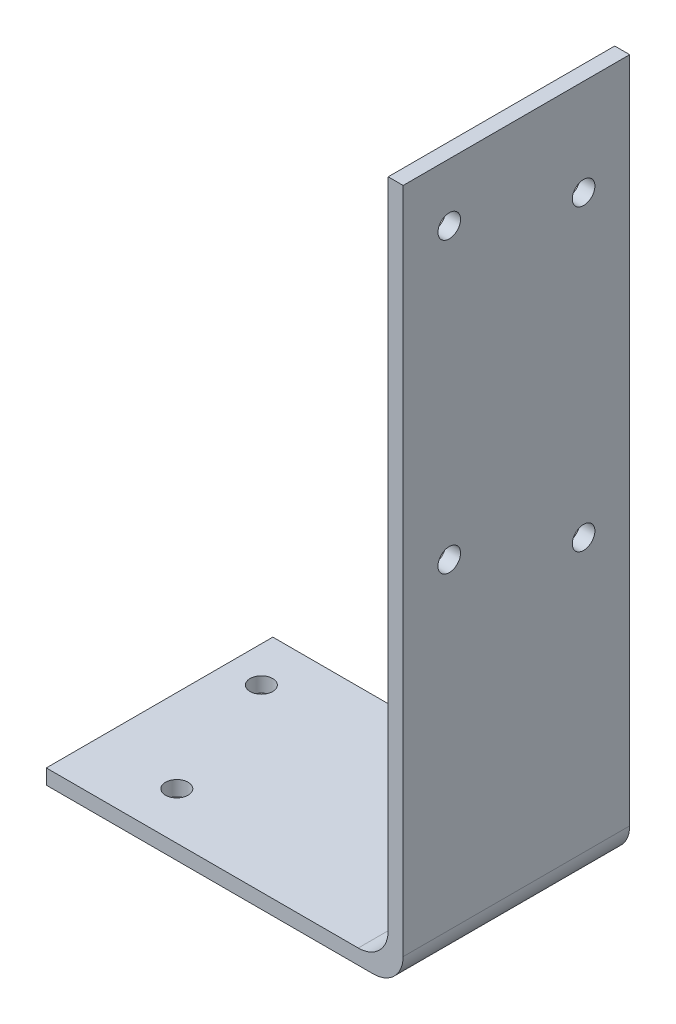
SolidWorks part; units mm, degrees
ref_plane "Front Plane" through (0, 0, 0) normal (0, 0, 1) x (1, 0, 0)
ref_plane "Top Plane" through (0, 0, 0) normal (0, 1, 0) x (1, 0, 0)
ref_plane "Right Plane" through (0, 0, 0) normal (1, 0, 0) x (0, 0, -1)
sketch "Sketch1" plane through (0, 0, 0) normal (0, 0, 1) x (1, 0, 0)
  line L0 (0, 0) -> (113.4872, 0)
  line L1 (113.4872, 0) -> (113.4872, 118.4148)
  line L2 (113.4872, 118.4148) -> (110.9472, 118.4148)
  line L3 (110.9472, 118.4148) -> (110.9472, 2.54)
  line L4 (110.9472, 2.54) -> (0, 2.54)
  line L5 (0, 2.54) -> (0, 0)
  dimension "D1" = 2.54
  dimension "D2" = 113.4872
  dimension "D3" = 118.4148
extrude "Boss-Extrude1" add sketch "Sketch1" along normal blind 38.4429
sketch "Sketch2" plane through (0, 2.54, 0) normal (0, 1, 0) x (1, 0, 0)
  line L0 (16.2052, -38.4429) -> (16.2052, -30.4292) construction
  line L1 (110.9472, -38.4429) -> (0, -38.4429) construction
  line L2 (16.2052, -30.4292) -> (67.0687, -30.4292) construction
  line L3 (9.8806, 0) -> (9.8806, -8.0137) construction
  line L4 (110.9472, 0) -> (0, 0) construction
  line L5 (9.8806, -8.0137) -> (59.0042, -8.0137) construction
  line L6 (113.4872, -38.4429) -> (113.4872, 0) construction
  circle A0 centre (67.0687, -30.4292) radius 1.9177
  circle A1 centre (59.0042, -8.0137) radius 1.9177
  circle A2 centre (16.2052, -30.4292) radius 1.9177
  circle A3 centre (9.8806, -8.0137) radius 1.9177
  dimension "D2" = 3.8354
  dimension "D1" = 8.0137
  dimension "D3" = 46.4185
  dimension "D4" = 54.483
  dimension "D5" = 97.282
  dimension "D6" = 103.6066
extrude "Cut-Extrude1" cut sketch "Sketch2" against normal through all
sketch "Sketch3" plane through (110.9472, 0, 0) normal (-1, 0, 0) x (0, 0, 1)
  line L0 (0, 4.9657) -> (38.4429, 4.9657) construction
  line L1 (0, 118.4148) -> (0, 2.54) construction
  line L2 (38.4429, 118.4148) -> (38.4429, 2.54) construction
  line L3 (38.4429, 0) -> (0, 0) construction
  line L4 (0, 102.0699) -> (7.8232, 102.0699) construction
  line L5 (7.8232, 102.0699) -> (7.8232, 51.3842) construction
  line L6 (38.4429, 108.5723) -> (30.6197, 108.5723) construction
  line L7 (30.6197, 108.5723) -> (30.6197, 59.5249) construction
  circle A0 centre (7.8232, 51.3842) radius 1.9177
  circle A1 centre (30.6197, 59.5249) radius 1.9177
  circle A2 centre (7.8232, 102.0699) radius 1.9177
  circle A3 centre (30.6197, 108.5723) radius 1.9177
  dimension "D3" = 3.8354
  dimension "D1" = 4.9657
  dimension "D2" = 7.8232
  dimension "D4" = 46.4185
  dimension "D5" = 54.5592
  dimension "D6" = 97.1042
  dimension "D7" = 103.6066
extrude "Cut-Extrude2" cut sketch "Sketch3" against normal through all
fillet "Fillet1" radius 5.08 2 edges at (110.9472, 2.54, 19.2215) (113.4872, 0, 19.2215)
sketch "Sketch4" plane through (0, 2.54, 0) normal (0, 1, 0) x (1, 0, 0)
  line L0 (52.9336, 0) -> (52.9336, -38.4429)
  line L1 (105.8672, 0) -> (0, 0) construction
  line L2 (105.8672, -38.4429) -> (0, -38.4429) construction
  line L3 (52.9336, -38.4429) -> (0, -38.4429)
  line L4 (0, -38.4429) -> (0, 0)
  line L5 (0, 0) -> (52.9336, 0)
extrude "Cut-Extrude4" cut sketch "Sketch4" against normal through all
sketch "Sketch5" plane through (110.9472, 0, 0) normal (-1, 0, 0) x (0, 0, 1)
  line L0 (0, 118.4148) -> (38.4429, 118.4148) construction
  point P4 (19.2215, 118.4148)
ref_plane "Center plane" through (0, 0, 19.2215) normal (0, 0, 1) x (1, 0, 0)
